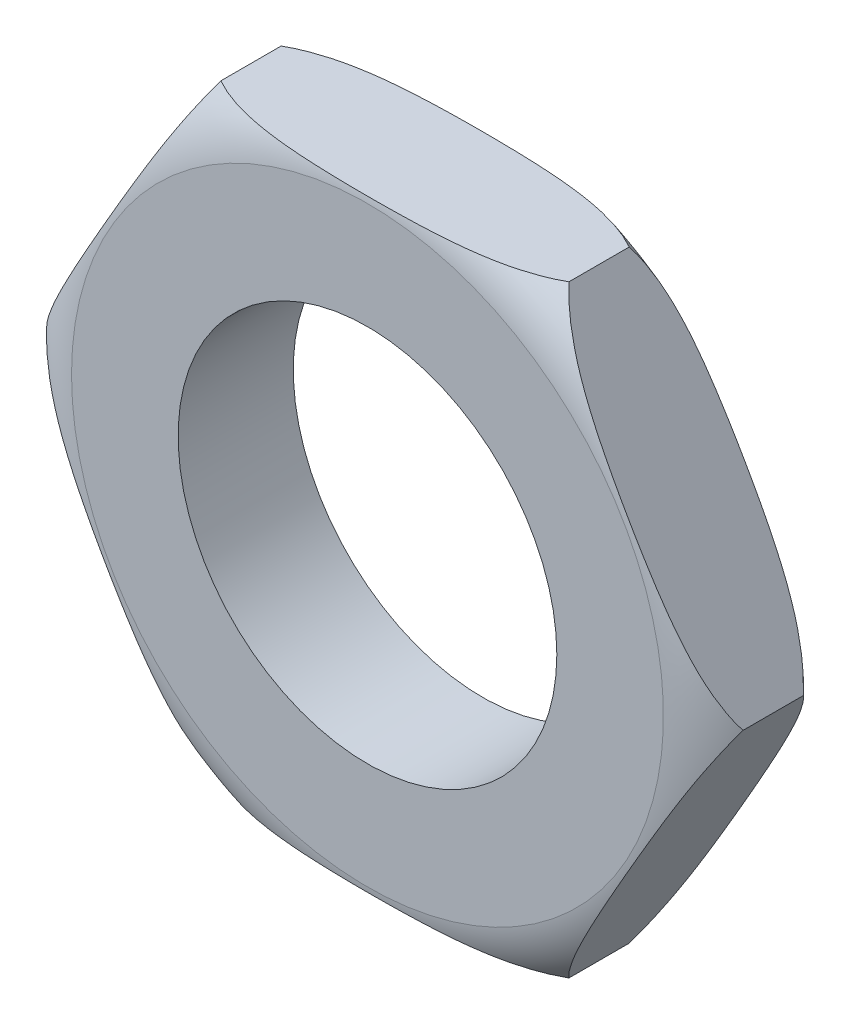
SolidWorks part; units mm, degrees
material "Plain Carbon Steel"
ref_plane "Front Plane" through (0, 0, 0) normal (0, 0, 1) x (1, 0, 0)
ref_plane "Top Plane" through (0, 0, 0) normal (0, 1, 0) x (1, 0, 0)
ref_plane "Right Plane" through (0, 0, 0) normal (1, 0, 0) x (0, 0, -1)
sketch "Sketch2" plane through (0, 0, 0) normal (0, 0, 1) x (1, 0, 0)
  line L0 (-6.3509, 0) -> (6.3509, 0) construction
  line L1 (-3.1754, -5.5) -> (3.1754, -5.5)
  line L2 (3.1754, -5.5) -> (6.3509, 0)
  line L3 (6.3509, 0) -> (3.1754, 5.5)
  line L4 (3.1754, 5.5) -> (-3.1754, 5.5)
  line L5 (-3.1754, 5.5) -> (-6.3509, 0)
  line L6 (-6.3509, 0) -> (-3.1754, -5.5)
  circle A0 centre (0, 0) radius 5.5 construction
  dimension "D1" = 11
extrude "Boss-Extrude1" add sketch "Sketch2" along normal mid plane 2.1
hole_wizard "5/16-24 Tapped Hole1" positions "Sketch3" profile "Sketch5" tap size "5/16-24" standard "ANSI Inch" end condition through all
sketch "Sketch3" plane through (0, 0, 1.05) normal (0, 0, 1) x (1, 0, 0)
  point P0 (0, 0)
sketch "Sketch5" plane through (0, 0, 1.05) normal (1, 0, 0) x (0, -1, 0)
  line L0 (0, 0) -> (0, 2.1)
  line L1 (0, 2.1) -> (3.4544, 2.1)
  line L2 (3.4544, 2.1) -> (3.4544, 0)
  line L5 (3.4544, 0) -> (0, 0)
  line L11 (0, -6.35) -> (0, 107.95) construction
  dimension "Thru Tap Drill Dia." = 6.9088
  dimension "Thru Tap Drill Depth" = 2.1
cosmetic thread "Hole Thread1" parameters "D2"=7.9375
sketch "Sketch7" plane through (0, 0, 0) normal (0, 1, 0) x (1, 0, 0)
  line L0 (-6.3509, -0.55) -> (-6.3509, -1.05)
  line L1 (-6.3509, -1.05) -> (-5.4, -1.05)
  line L2 (0, 0) -> (0, -2.9107) construction
  line L3 (0, 1.05) -> (0, -1.05) construction
  arc A0 (-6.3509, -0.55) -> (-5.4, -1.05) centre (-5.2236, 0.4396) ccw
  point P9 (-6.663, -0.55)
  point P10 (-6.3509, -1.05)
  dimension "D3" = 1.5
  dimension "D1" = 10.8
  dimension "D2" = 0.5
revolve "Cut-Revolve2" cut sketch "Sketch7" angle 360 about L2
mirror "Mirror1" about plane through (0, 0, 0) normal (0, 0, 1) of "Cut-Revolve2"
